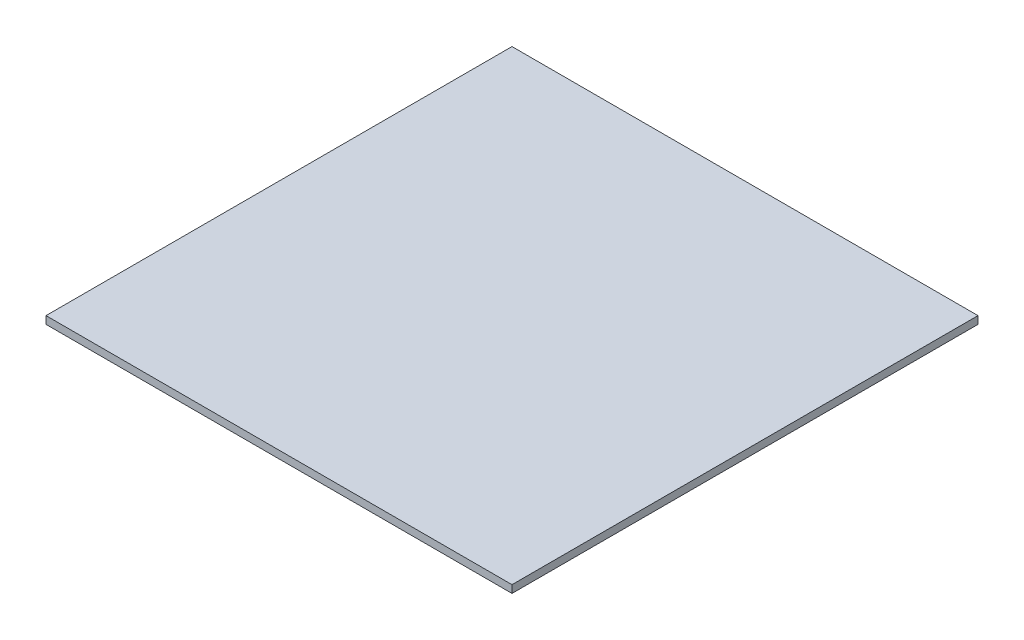
SolidWorks part; units mm, degrees
ref_plane "Front Plane" through (0, 0, 0) normal (0, 0, 1) x (1, 0, 0)
ref_plane "Top Plane" through (0, 0, 0) normal (0, 1, 0) x (1, 0, 0)
ref_plane "Right Plane" through (0, 0, 0) normal (1, 0, 0) x (0, 0, -1)
sketch "Sketch1" plane through (0, 0, 0) normal (0, 1, 0) x (1, 0, 0)
  line L1 (0, 0) -> (381, 0)
  line L2 (0, 0) -> (0, 381)
  line L3 (0, 381) -> (381, 381)
  line L4 (381, 0) -> (381, 381)
  dimension "D1" = 381
  dimension "D2" = 381
extrude "Boss-Extrude1" add sketch "Sketch1" along normal blind 6.223
